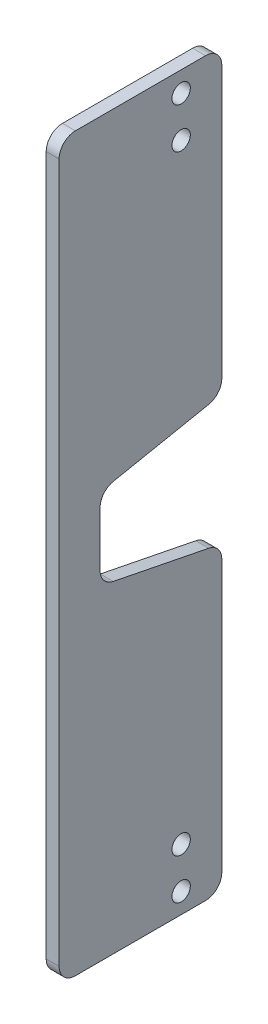
SolidWorks part; units mm, degrees
ref_plane "前视基准面" through (0, 0, 0) normal (0, 0, 1) x (1, 0, 0)
ref_plane "上视基准面" through (0, 0, 0) normal (0, 1, 0) x (1, 0, 0)
ref_plane "右视基准面" through (0, 0, 0) normal (1, 0, 0) x (0, 0, -1)
ref_plane "基准面4" through (-0.7938, 0, 0) normal (-1, 0, 0) x (0, -1, 0)
sketch "草图1" plane through (-0.7938, 0, 0) normal (-1, 0, 0) x (0, -1, 0)
  line L1 (38.795, 5) -> (12.795, 5)
  line L2 (10.795, 3) -> (10.795, -13)
  line L5 (10.795, 3) -> (55.77, 3) construction
  line L6 (55.77, 3) -> (55.77, -5.0783) construction
  line L7 (55.77, 3) -> (55.77, 5) construction
  line L13 (38.795, 5) -> (72.745, 5)
  line L15 (100.745, 3) -> (100.745, -13)
  line L18 (72.745, 5) -> (98.745, 5)
  line L19 (55.77, 5) -> (55.77, -5.0783) construction
  line L20 (55.77, -5.0783) -> (55.77, -0.0391) construction
  line L21 (55.77, -0.0391) -> (65.77, -0.0391) construction
  line L22 (72.112, -14.1547) -> (62.1308, -0.0391) construction
  line L31 (13.295, -15) -> (13.295, -10) construction
  line L32 (13.295, 0) -> (13.295, -15) construction
  line L33 (18.295, 0) -> (18.295, -15) construction
  line L34 (18.295, -15) -> (18.295, -10) construction
  line L35 (93.245, 0) -> (93.245, -15) construction
  line L36 (93.245, -15) -> (93.245, -10) construction
  line L37 (93.245, -10) -> (98.245, -10) construction
  line L38 (55.77, -0.0391) -> (50.77, -0.0391)
  line L39 (55.77, -0.0391) -> (60.77, -0.0391)
  line L40 (12.795, -15) -> (47.795, -15)
  line L41 (98.745, -15) -> (63.745, -15)
  line L42 (50.77, -0.0391) -> (47.795, -15)
  line L43 (60.77, -0.0391) -> (63.745, -15)
  arc A2 (12.795, 5) -> (10.795, 3) centre (12.795, 3) ccw
  arc A3 (10.795, -13) -> (12.795, -15) centre (12.795, -13) ccw
  arc A12 (98.745, 5) -> (100.745, 3) centre (98.745, 3) cw
  arc A13 (100.745, -13) -> (98.745, -15) centre (98.745, -13) cw
  circle A17 centre (13.295, -10) radius 1.1303
  circle A18 centre (18.295, -10) radius 1.1303
  circle A19 centre (93.245, -10) radius 1.1303
  circle A20 centre (98.245, -10) radius 1.1303
extrude "凸台-拉伸1" add sketch "草图1" against normal blind 1.588
fillet "圆角1" radius 2 1 edges at (0.0003, -47.795, -15)
fillet "圆角2" radius 2 1 edges at (0.0002, -50.77, -0.0391)
fillet "圆角3" radius 2 1 edges at (0.0002, -60.77, -0.0391)
fillet "圆角4" radius 2 1 edges at (0.0003, -63.745, -15)
